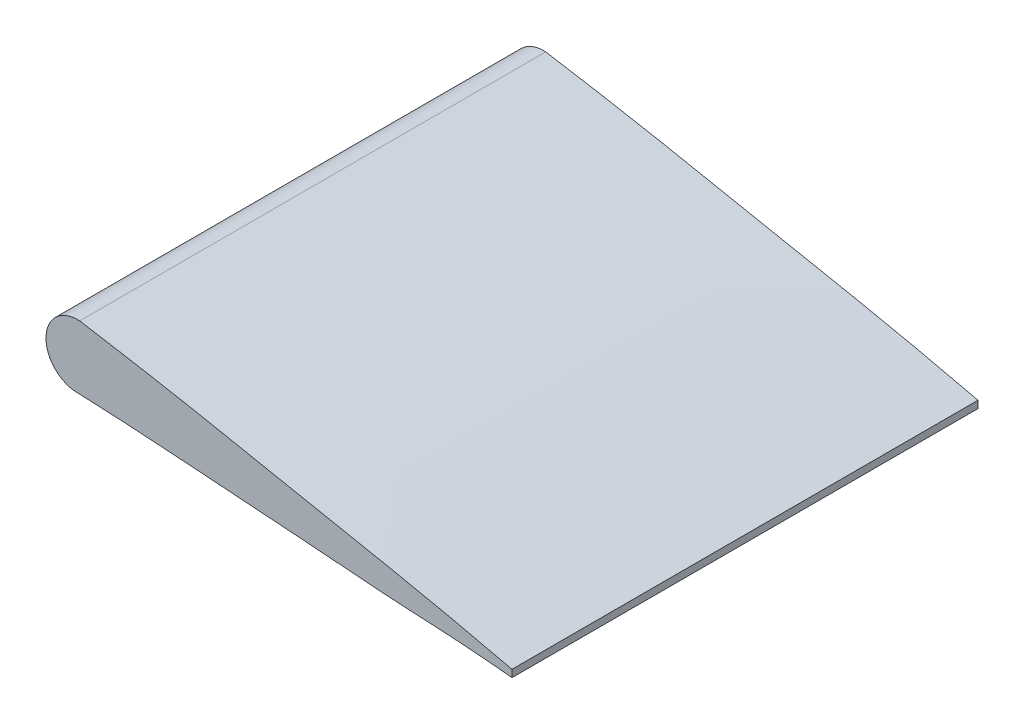
SolidWorks part; units mm, degrees
ref_plane "Front Plane" through (0, 0, 0) normal (0, 0, 1) x (1, 0, 0)
ref_plane "Top Plane" through (0, 0, 0) normal (0, 1, 0) x (1, 0, 0)
ref_plane "Right Plane" through (0, 0, 0) normal (1, 0, 0) x (0, 0, -1)
curve "Curve1"
  spline degree 3 poles (25.4, 0.0889, 0) (24.9755, 0.1879, 0) (24.1284, 0.3854, 0) (22.4316, 0.7474, 0) (20.3056, 1.1527, 0) (17.7661, 1.6728, 0) (15.2225, 2.1285, 0) (12.6828, 2.5208, 0) (10.1333, 2.7153, 0) (7.5886, 2.7177, 0) (5.4641, 2.6194, 0) (3.7724, 2.3478, 0) (2.7142, 2.0863, 0) (1.8702, 1.7836, 0) (1.2225, 1.4719, 0) (0.6864, 1.0854, 0) (0.2512, 0.6226, 0) (-0.1733, 0.0898, 0) (0.2557, -0.4257, 0) (0.7562, -0.3188, 0) (1.2698, -0.1979, 0) (1.905, -0.0426, 0) (2.7433, 0.1487, 0) (3.8055, 0.2872, 0) (5.4925, 0.5064, 0) (7.6119, 0.6227, 0) (10.1512, 0.7472, 0) (12.6929, 0.6952, 0) (15.2354, 0.6324, 0) (17.7755, 0.4534, 0) (20.3173, 0.2785, 0) (22.4335, 0.1017, 0) (24.1313, 0.0327, 0) (24.9769, -0.0484, 0) (25.4, -0.0889, 0) knots 0 0 0 0 0.025045 0.049982 0.099693 0.149405 0.198931 0.248178 0.297011 0.345669 0.394384 0.418982 0.444018 0.456913 0.470405 0.485361 0.494029 0.508284 0.517562 0.523649 0.536105 0.548579 0.561002 0.585562 0.610033 0.658766 0.707435 0.756094 0.804785 0.853571 0.902386 0.951201 0.975578 1 1 1 1
sketch "Sketch1" plane through (0, 0, 0) normal (0, 0, 1) x (1, 0, 0)
  line L0 (25.4, 0.0889) -> (25.4, -0.0889) construction
  line L1 (254, 0.889) -> (254, -0.889)
  line L2 (0, 0) -> (254, 0) construction
  line L3 (127, 0) -> (127, 24.8566) construction
  line L4 (139.7, 0) -> (139.7, 6.6099) construction
  line L5 (139.7, 6.6099) -> (139.7, 23.1662)
  line L6 (147.4934, 14.1005) -> (147.4934, 0) construction
  arc A0 (147.9779, 6.3222) -> (147.9779, 21.8788) centre (147.4934, 14.1005) cw
  spline S0 degree 3 poles (566.0092, 1924.6845) (86.0699, -40.1547) (57.6216, -6.7602) (22.4316, 0.7474) (20.3056, 1.1527) (17.7661, 1.6728) (15.2225, 2.1285) (12.6828, 2.5208) (10.1333, 2.7153) (7.5886, 2.7177) (5.4641, 2.6194) (3.7724, 2.3478) (2.7142, 2.0863) (1.8702, 1.7836) (1.2225, 1.4719) (0.6864, 1.0854) (0.2512, 0.6226) (-0.1733, 0.0898) (0.2557, -0.4257) (0.7562, -0.3188) (1.2698, -0.1979) (1.905, -0.0426) (2.7433, 0.1487) (3.8055, 0.2872) (5.4925, 0.5064) (7.6119, 0.6227) (10.1512, 0.7472) (12.6929, 0.6952) (15.2354, 0.6324) (17.7755, 0.4534) (20.3173, 0.2785) (22.4335, 0.1017) (47.7216, -0.9264) (69.4681, -40.4772) (235.2289, 1988.3291) knots -1.967795 -1.967795 -1.967795 -1.967795 0.025045 0.049982 0.099693 0.149405 0.198931 0.248178 0.297011 0.345669 0.394384 0.418982 0.444018 0.456913 0.470405 0.485361 0.494029 0.508284 0.517562 0.523649 0.536105 0.548579 0.561002 0.585562 0.610033 0.658766 0.707435 0.756094 0.804785 0.853571 0.902386 0.951201 0.975578 2.356301 2.356301 2.356301 2.356301 only from (25.4, 0.0889) to (25.4, -0.0889) construction
  spline S1 degree 3 poles (25.4, 0.0889) (24.9755, 0.1879) (24.1284, 0.3854) (22.4316, 0.7474) (20.3056, 1.1527) (17.7661, 1.6728) (15.2225, 2.1285) (12.6828, 2.5208) (10.1333, 2.7153) (7.5886, 2.7177) (5.4641, 2.6194) (3.7724, 2.3478) (2.7142, 2.0863) (1.8702, 1.7836) (1.2225, 1.4719) (0.6864, 1.0854) (0.2512, 0.6226) (-0.1733, 0.0898) (0.2557, -0.4257) (0.7562, -0.3188) (1.2698, -0.1979) (1.905, -0.0426) (2.7433, 0.1487) (3.8055, 0.2872) (5.4925, 0.5064) (7.6119, 0.6227) (10.1512, 0.7472) (12.6929, 0.6952) (15.2354, 0.6324) (17.7755, 0.4534) (20.3173, 0.2785) (22.4335, 0.1017) (24.1313, 0.0327) (24.9769, -0.0484) (25.4, -0.0889) knots 0 0 0 0 0.025045 0.049982 0.099693 0.149405 0.198931 0.248178 0.297011 0.345669 0.394384 0.418982 0.444018 0.456913 0.470405 0.485361 0.494029 0.508284 0.517562 0.523649 0.536105 0.548579 0.561002 0.585562 0.610033 0.658766 0.707435 0.756094 0.804785 0.853571 0.902386 0.951201 0.975578 1 1 1 1 construction
  spline S2 degree 3 poles (254, 0.889) (249.7553, 1.8786) (241.2842, 3.8535) (224.3158, 7.4736) (203.0565, 11.5272) (177.6613, 16.7283) (152.2253, 21.2846) (126.8284, 25.208) (101.3332, 27.1529) (75.8856, 27.1773) (54.6411, 26.1945) (37.7241, 23.4783) (27.1418, 20.8628) (18.7017, 17.8364) (12.2246, 14.7192) (6.8643, 10.8535) (2.5124, 6.2258) (-1.7329, 0.8975) (2.5571, -4.257) (7.5624, -3.188) (12.6982, -1.9788) (19.0498, -0.4259) (27.4332, 1.4865) (38.0551, 2.8725) (54.9249, 5.0635) (76.1187, 6.227) (101.5119, 7.4722) (126.9288, 6.9519) (152.354, 6.3244) (177.755, 4.534) (203.1733, 2.7851) (224.3353, 1.0168) (241.3134, 0.3266) (249.7685, -0.4836) (254, -0.889) knots 0 0 0 0 0.025045 0.049982 0.099693 0.149405 0.198931 0.248178 0.297011 0.345669 0.394384 0.418982 0.444018 0.456913 0.470405 0.485361 0.494029 0.508284 0.517562 0.523649 0.536105 0.548579 0.561002 0.585562 0.610033 0.658766 0.707435 0.756094 0.804785 0.853571 0.902386 0.951201 0.975578 1 1 1 1
  point P9 (139.7, 0)
  point P12 (139.7, 14.888)
  point P14 (147.9779, 6.3222)
  dimension "D1" = 254
  dimension "D2" = 24.8566
  dimension "D3" = 139.7
  dimension "D4" = 8.2779
extrude "Boss-Extrude1" add sketch "Sketch1" along normal blind 114.3 contours L1 S2 A0
